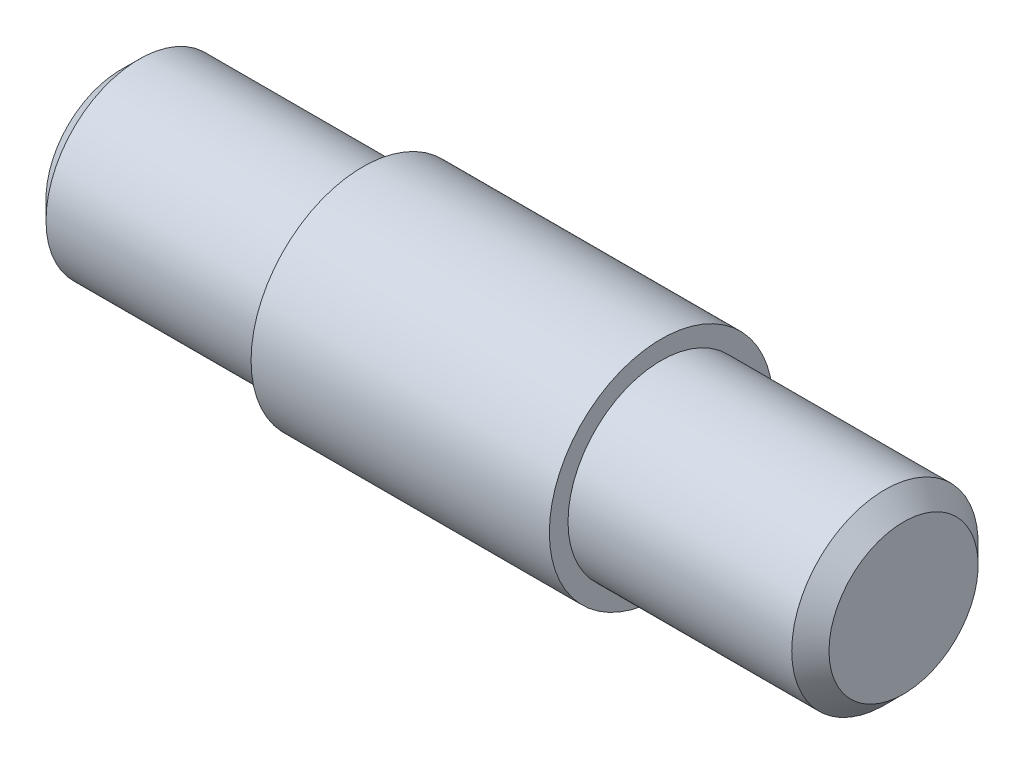
SolidWorks part; units mm, degrees
material "Alliage 7079"
ref_plane "Face" through (0, 0, 0) normal (0, 0, 1) x (1, 0, 0)
ref_plane "Dessus" through (0, 0, 0) normal (0, 1, 0) x (1, 0, 0)
ref_plane "Droite" through (0, 0, 0) normal (1, 0, 0) x (0, 0, -1)
sketch "Esquisse1" plane through (0, 0, 0) normal (0, 0, 1) x (1, 0, 0)
  line L0 (-54.8246, 0) -> (50.8422, 0) construction
  line L1 (0, 0) -> (0, 2.5)
  line L2 (0, 2.5) -> (6.5, 2.5)
  line L3 (6.5, 2.5) -> (6.5, 3)
  line L4 (6.5, 3) -> (14.5, 3)
  line L5 (14.5, 3) -> (14.5, 2.5)
  line L6 (14.5, 2.5) -> (21, 2.5)
  line L7 (21, 2.5) -> (21, 0)
  line L8 (21, 0) -> (0, 0)
  dimension "D1" = 3
  dimension "D2" = 2.5
  dimension "D3" = 2.5
  dimension "D4" = 21
  dimension "D5" = 6.5
  dimension "D6" = 6.5
revolve "Révolution1" add sketch "Esquisse1" angle 360 about L0
chamfer "Chanfrein1" distance 0.5 angle 45 2 edges at (21, 0, 2.5) (0, 0, 2.5)
